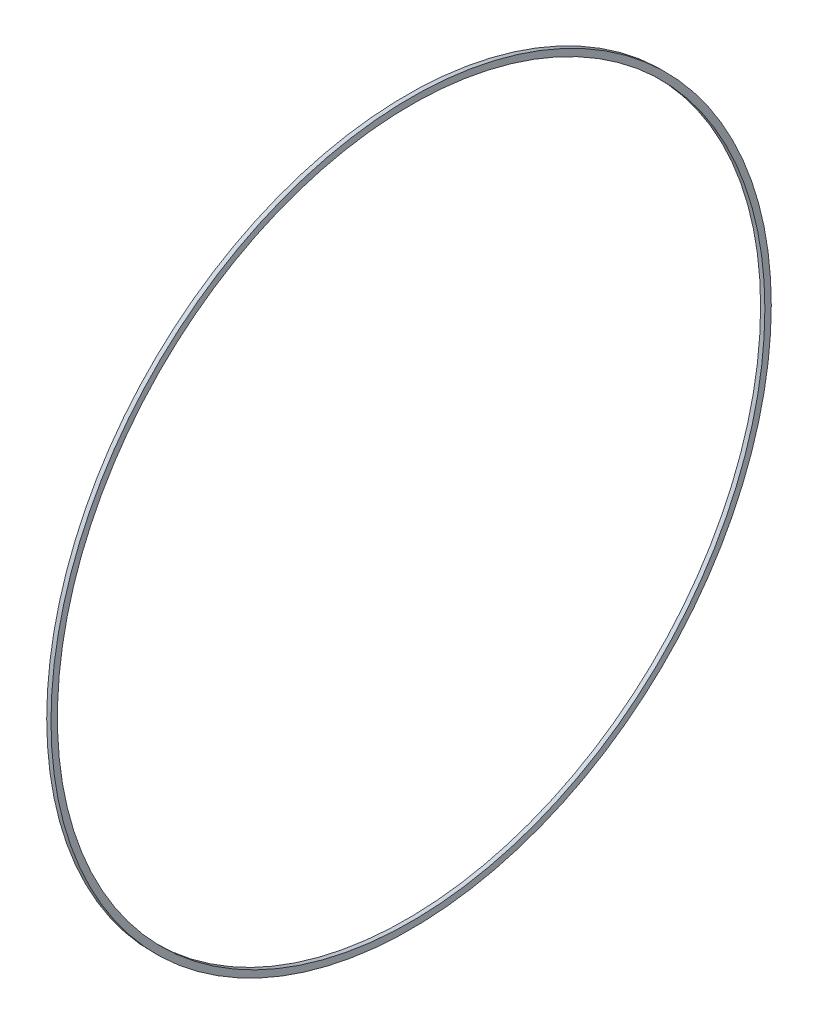
SolidWorks part; units mm, degrees
ref_plane "Front Plane" through (0, 0, 0) normal (0, 0, 1) x (1, 0, 0)
ref_plane "Top Plane" through (0, 0, 0) normal (0, 1, 0) x (1, 0, 0)
ref_plane "Right Plane" through (0, 0, 0) normal (1, 0, 0) x (0, 0, -1)
sketch "Sketch1" plane through (0, 0, 0) normal (1, 0, 0) x (0, 0, -1)
  circle A0 centre (0, 0) radius 168.5
  circle A1 centre (0, 0) radius 165.5
extrude "Boss-Extrude1" add sketch "Sketch1" along normal blind 2
